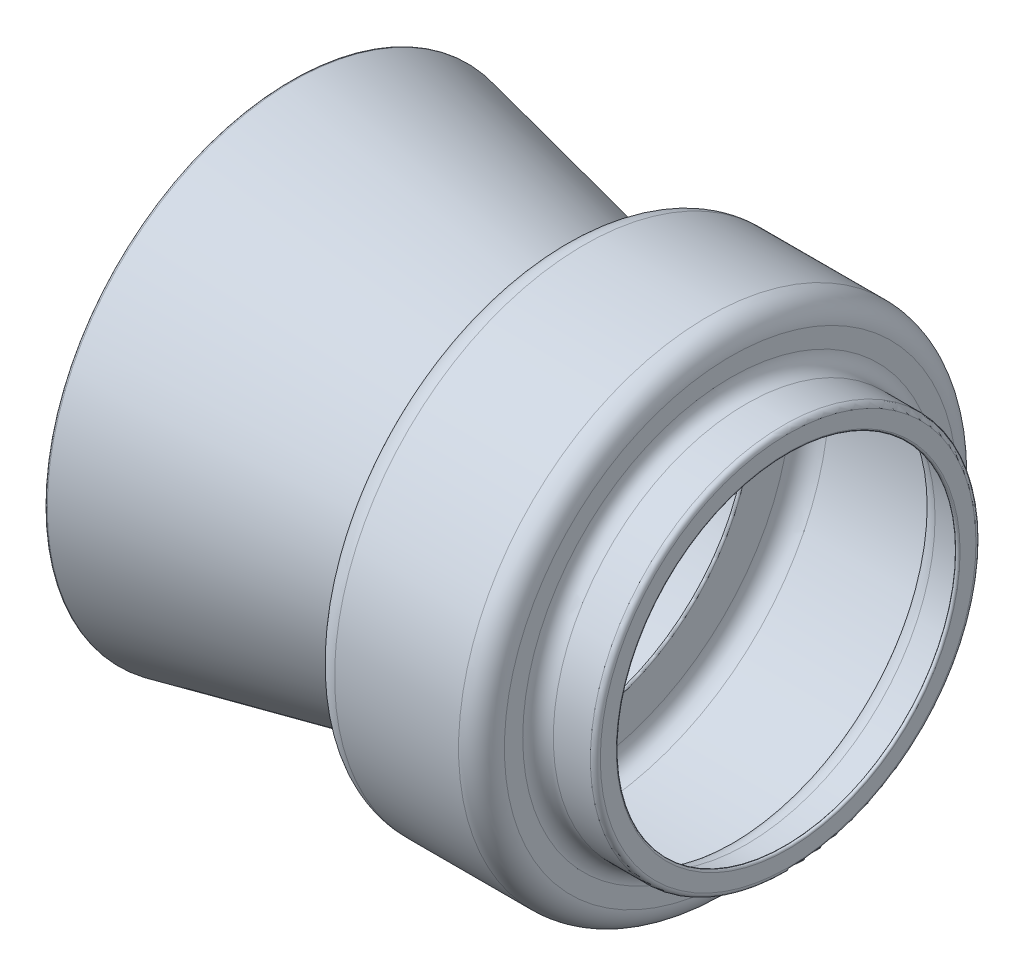
SolidWorks part; units mm, degrees
ref_plane "Front Plane" through (0, 0, 0) normal (0, 0, 1) x (1, 0, 0)
ref_plane "Top Plane" through (0, 0, 0) normal (0, 1, 0) x (1, 0, 0)
ref_plane "Right Plane" through (0, 0, 0) normal (1, 0, 0) x (0, 0, -1)
sketch "Sketch1" plane through (0, 0, 0) normal (0, 0, 1) x (1, 0, 0)
  line L0 (0, 45) -> (0, 49.15)
  line L1 (-1.3, 50.45) -> (-11, 50.45)
  line L2 (-15, 54.45) -> (-15, 59.25)
  line L3 (-21, 65.25) -> (-53.44, 65.25)
  line L4 (-59.44, 59.25) -> (-59.44, 49.57)
  line L5 (-59.44, 49.57) -> (-129.44, 64.449)
  line L6 (-1, 45) -> (-1, 49.15)
  line L7 (-1.3, 49.45) -> (-11, 49.45)
  line L8 (-16, 54.45) -> (-16, 59.25)
  line L9 (-21, 64.25) -> (-53.44, 64.25)
  line L10 (-58.44, 59.25) -> (-58.44, 48.9526)
  line L11 (-59.044, 48.4635) -> (-129.6479, 63.4708)
  line L12 (-129.44, 64.449) -> (-129.6479, 63.4708) construction
  line L13 (-1, 45) -> (0, 45) construction
  line L14 (0, 0) -> (0, 45) construction
  line L15 (-58.44, 59.25) -> (-58.44, 48.3351) construction
  line L16 (-58.44, 48.3351) -> (-129.6479, 63.4708) construction
  line L17 (0, 0) -> (-92.0192, 0) construction
  arc A0 (0, 49.15) -> (-1.3, 50.45) centre (-1.3, 49.15) ccw
  arc A1 (-11, 50.45) -> (-15, 54.45) centre (-11, 54.45) cw
  arc A2 (-15, 59.25) -> (-21, 65.25) centre (-21, 59.25) ccw
  arc A3 (-53.44, 65.25) -> (-59.44, 59.25) centre (-53.44, 59.25) ccw
  arc A4 (-1, 49.15) -> (-1.3, 49.45) centre (-1.3, 49.15) ccw
  arc A5 (-11, 49.45) -> (-16, 54.45) centre (-11, 54.45) cw
  arc A6 (-16, 59.25) -> (-21, 64.25) centre (-21, 59.25) ccw
  arc A7 (-53.44, 64.25) -> (-58.44, 59.25) centre (-53.44, 59.25) ccw
  arc A8 (-129.44, 64.449) -> (-129.6479, 63.4708) centre (-129.544, 63.9599) ccw
  arc A9 (-1, 45) -> (0, 45) centre (-0.5, 45) ccw
  arc A10 (-58.44, 48.9526) -> (-59.044, 48.4635) centre (-58.94, 48.9526) cw
  point P10 (0, 50.45)
  point P13 (-15, 50.45)
  point P16 (-15, 65.25)
  point P19 (-59.44, 65.25)
  dimension "D8" = 1.3
  dimension "D9" = 4
  dimension "D10" = 6
  dimension "D11" = 6
  dimension "D14" = 0.5
  dimension "D1" = 78
  dimension "D2" = 5.45
  dimension "D3" = 15
  dimension "D4" = 14.8
  dimension "D5" = 44.44
  dimension "D6" = 15.68
  dimension "D7" = 70
  dimension "D13" = 45
  dimension "D12" = 1
revolve "Revolve1" add sketch "Sketch1" angle 360 about L17
scale "Scale1" scale about centroid uniform scaling yes scale factor 10
scale "Scale2" scale about origin uniform scaling yes scale factor 0.75
